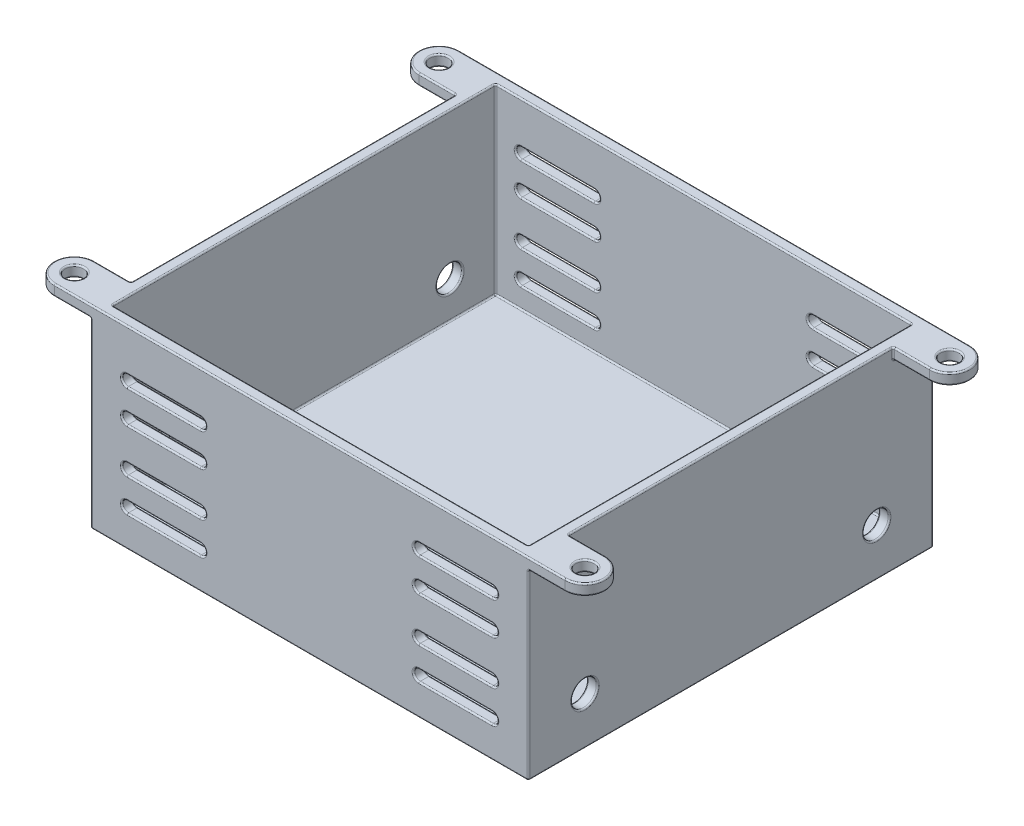
SolidWorks part; units mm, degrees
ref_plane "Front Plane" through (0, 0, 0) normal (0, 0, 1) x (1, 0, 0)
ref_plane "Top Plane" through (0, 0, 0) normal (0, 1, 0) x (1, 0, 0)
ref_plane "Right Plane" through (0, 0, 0) normal (1, 0, 0) x (0, 0, -1)
sketch "Sketch1" plane through (0, 0, 0) normal (0, 1, 0) x (1, 0, 0)
  line L0 (-35, 27.75) -> (35, 27.75) construction
  line L1 (-35, 25) -> (35, 25) construction
  line L2 (-35, 25) -> (-35, -25) construction
  line L3 (-35, -25) -> (35, -25) construction
  line L4 (35, 25) -> (35, -25) construction
  line L5 (-35, 25) -> (35, -25) construction
  line L6 (-35, -25) -> (35, 25) construction
  line L7 (-35, -27.75) -> (35, -27.75) construction
  line L8 (37.75, 25) -> (37.75, -25) construction
  line L9 (-37.75, 25) -> (-37.75, -25) construction
  line L10 (-35, 27.75) -> (-30, 27.75)
  line L11 (-30, 27.75) -> (30, 27.75)
  line L12 (-30, 27.75) -> (-30, -27.75)
  line L13 (-30, -27.75) -> (30, -27.75)
  line L14 (30, 27.75) -> (30, -27.75)
  line L15 (-30, 27.75) -> (30, -27.75) construction
  line L16 (-30, -27.75) -> (30, 27.75) construction
  line L17 (-35, 22.25) -> (-30, 22.25)
  line L18 (35, 27.75) -> (30, 27.75)
  line L19 (35, 22.25) -> (30, 22.25)
  line L20 (30, -27.75) -> (35, -27.75)
  line L21 (35, -22.25) -> (30, -22.25)
  line L22 (-35, -22.25) -> (-30, -22.25)
  line L23 (-35, -27.75) -> (-30, -27.75)
  circle A0 centre (-35, 25) radius 1.25
  circle A1 centre (35, 25) radius 1.25
  circle A2 centre (35, -25) radius 1.25
  circle A3 centre (-35, -25) radius 1.25
  circle A4 centre (35, 25) radius 2.75
  circle A5 centre (35, -25) radius 2.75
  circle A6 centre (-35, -25) radius 2.75
  circle A7 centre (-35, 25) radius 2.75
  point P0 (0, 0)
  point P27 (0, 0)
  dimension "D3" = 2.5
  dimension "D1" = 70
  dimension "D2" = 50
  dimension "D5" = 60
  dimension "D4" = 1.5
sketch "Sketch2" plane through (0, 0, 0) normal (0, 1, 0) x (1, 0, 0)
  line L10 (-30, 27.75) -> (-30, -27.75) construction
  line L11 (-30, -27.75) -> (30, -27.75) construction
  line L12 (30, 27.75) -> (30, -27.75) construction
  line L13 (-30, 27.75) -> (30, 27.75) construction
  line L14 (-28.5, 26.25) -> (-28.5, -26.25)
  line L15 (-28.5, -26.25) -> (28.5, -26.25)
  line L16 (28.5, -26.25) -> (28.5, 26.25)
  line L17 (28.5, 26.25) -> (-28.5, 26.25)
  line L18 (-28.5, 26.25) -> (-28.5, -26.25)
  line L19 (-28.5, -26.25) -> (28.5, -26.25)
  line L20 (28.5, -26.25) -> (28.5, 26.25)
  line L21 (28.5, 26.25) -> (-28.5, 26.25)
  line L22 (-30, 27.75) -> (-30, -27.75)
  line L23 (-30, -27.75) -> (30, -27.75)
  line L24 (30, 27.75) -> (30, -27.75)
  line L25 (-30, 27.75) -> (30, 27.75)
  dimension "D1" = 1.5
extrude "Boss-Extrude1" add sketch "Sketch2" against normal blind 25
sketch "Sketch3" plane through (0, -25, 0) normal (0, -1, 0) x (1, 0, 0)
  line L0 (30, -27.75) -> (-30, -27.75) construction
  line L1 (-30, -27.75) -> (-30, 27.75) construction
  line L2 (-30, 27.75) -> (30, 27.75) construction
  line L3 (30, 27.75) -> (30, -27.75) construction
  line L4 (30, -27.75) -> (-30, -27.75)
  line L5 (-30, -27.75) -> (-30, 27.75)
  line L6 (-30, 27.75) -> (30, 27.75)
  line L7 (30, 27.75) -> (30, -27.75)
extrude "Boss-Extrude2" add sketch "Sketch3" along normal blind 1.5
sketch "Sketch4" plane through (0, 0, 0) normal (0, 1, 0) x (1, 0, 0)
  line L0 (-35, -27.75) -> (-30, -27.75) construction
  line L1 (-35, -22.25) -> (-30, -22.25) construction
  line L2 (30, -27.75) -> (35, -27.75) construction
  line L3 (35, -22.25) -> (30, -22.25) construction
  line L4 (-35, 22.25) -> (-30, 22.25) construction
  line L5 (-35, 27.75) -> (-30, 27.75) construction
  line L6 (35, 22.25) -> (30, 22.25) construction
  line L7 (35, 27.75) -> (30, 27.75) construction
  line L8 (-35, -27.75) -> (-30, -27.75)
  line L9 (-35, -22.25) -> (-30, -22.25)
  line L10 (30, -27.75) -> (35, -27.75)
  line L11 (35, -22.25) -> (30, -22.25)
  line L12 (-35, 22.25) -> (-30, 22.25)
  line L13 (-35, 27.75) -> (-30, 27.75)
  line L14 (35, 22.25) -> (30, 22.25)
  line L15 (35, 27.75) -> (30, 27.75)
  line L16 (-30, 27.75) -> (-30, 22.25)
  line L17 (30, 27.75) -> (30, 22.25)
  line L18 (30, -22.25) -> (30, -27.75)
  line L19 (-30, -22.25) -> (-30, -27.75)
  circle A0 centre (-35, -25) radius 1.25 construction
  circle A1 centre (-35, -25) radius 2.75 construction
  circle A2 centre (35, -25) radius 1.25 construction
  circle A3 centre (35, -25) radius 2.75 construction
  circle A4 centre (-35, 25) radius 2.75 construction
  circle A5 centre (35, 25) radius 1.25 construction
  circle A6 centre (35, 25) radius 2.75 construction
  circle A7 centre (-35, -25) radius 1.25
  arc A8 (-35, -22.25) -> (-35, -27.75) centre (-35, -25) ccw
  circle A9 centre (35, -25) radius 1.25
  arc A10 (35, -27.75) -> (35, -22.25) centre (35, -25) ccw
  arc A11 (-35, 27.75) -> (-35, 22.25) centre (-35, 25) ccw
  circle A12 centre (35, 25) radius 1.25
  arc A13 (35, 22.25) -> (35, 27.75) centre (35, 25) ccw
  circle A14 centre (-35, 25) radius 1.25 construction
  circle A15 centre (-35, 25) radius 1.25
extrude "Boss-Extrude3" add sketch "Sketch4" against normal blind 1.5
sketch "Sketch5" plane through (0, 0, 0) normal (0, 0, 1) x (1, 0, 0)
  line L0 (-30, -14) -> (30, -14) construction
  line L1 (-30, -26.5) -> (-30, -1.5) construction
  line L2 (30, -26.5) -> (30, -1.5) construction
  line L3 (0, -14) -> (0, -21.8638) construction
  line L4 (-25, -6.5) -> (-15, -6.5) construction
  line L5 (-25, -5.75) -> (-15, -5.75)
  line L6 (-25, -7.25) -> (-15, -7.25)
  line L7 (-25, -11) -> (-15, -11) construction
  line L8 (-25, -10.25) -> (-15, -10.25)
  line L9 (-25, -11.75) -> (-15, -11.75)
  line L10 (-25, -21.5) -> (-15, -21.5) construction
  line L11 (-25, -22.25) -> (-15, -22.25)
  line L12 (-25, -20.75) -> (-15, -20.75)
  line L13 (-25, -17) -> (-15, -17) construction
  line L14 (-25, -17.75) -> (-15, -17.75)
  line L15 (-25, -16.25) -> (-15, -16.25)
  line L16 (25, -6.5) -> (15, -6.5) construction
  line L17 (25, -5.75) -> (15, -5.75)
  line L18 (25, -7.25) -> (15, -7.25)
  line L19 (25, -11) -> (15, -11) construction
  line L20 (25, -10.25) -> (15, -10.25)
  line L21 (25, -11.75) -> (15, -11.75)
  line L22 (25, -21.5) -> (15, -21.5) construction
  line L23 (25, -22.25) -> (15, -22.25)
  line L24 (25, -20.75) -> (15, -20.75)
  line L25 (25, -17) -> (15, -17) construction
  line L26 (25, -17.75) -> (15, -17.75)
  line L27 (25, -16.25) -> (15, -16.25)
  arc A0 (-25, -5.75) -> (-25, -7.25) centre (-25, -6.5) ccw
  arc A1 (-15, -7.25) -> (-15, -5.75) centre (-15, -6.5) ccw
  arc A2 (-25, -10.25) -> (-25, -11.75) centre (-25, -11) ccw
  arc A3 (-15, -11.75) -> (-15, -10.25) centre (-15, -11) ccw
  arc A4 (-25, -22.25) -> (-25, -20.75) centre (-25, -21.5) cw
  arc A5 (-15, -20.75) -> (-15, -22.25) centre (-15, -21.5) cw
  arc A6 (-25, -17.75) -> (-25, -16.25) centre (-25, -17) cw
  arc A7 (-15, -16.25) -> (-15, -17.75) centre (-15, -17) cw
  arc A8 (25, -5.75) -> (25, -7.25) centre (25, -6.5) cw
  arc A9 (15, -7.25) -> (15, -5.75) centre (15, -6.5) cw
  arc A10 (25, -10.25) -> (25, -11.75) centre (25, -11) cw
  arc A11 (15, -11.75) -> (15, -10.25) centre (15, -11) cw
  arc A12 (25, -22.25) -> (25, -20.75) centre (25, -21.5) ccw
  arc A13 (15, -20.75) -> (15, -22.25) centre (15, -21.5) ccw
  arc A14 (25, -17.75) -> (25, -16.25) centre (25, -17) ccw
  arc A15 (15, -16.25) -> (15, -17.75) centre (15, -17) ccw
  point P11 (-20, -6.5)
  point P17 (-20, -11)
  point P25 (-20, -21.5)
  point P32 (-20, -17)
  point P39 (20, -6.5)
  point P46 (20, -11)
  point P53 (20, -21.5)
  point P60 (20, -17)
  dimension "D1" = 20
  dimension "D2" = 1.5
  dimension "D3" = 10
  dimension "D4" = 7.5
  dimension "D5" = 4.5
extrude "Cut-Extrude1" cut sketch "Sketch5" against normal through all both and the other way through all
sketch "Sketch6" plane through (0, 0, 0) normal (1, 0, 0) x (0, 0, -1)
  line L0 (0, 0) -> (0, -20) construction
  line L1 (0, -20) -> (-20, -20) construction
  circle A0 centre (-20, -20) radius 1.75
  circle A1 centre (20, -20) radius 1.75
  dimension "D1" = 20
  dimension "D3" = 3.5
  dimension "D2" = 20
extrude "Cut-Extrude2" cut sketch "Sketch6" against normal through all both and the other way through all
fillet "Fillet1" radius 0.2 196 edges at (25.75, -6.5, 26.25) (20, -7.25, 26.25) (14.25, -6.5, 26.25) (20, -5.75, 26.25) (-25.75, -17, 26.25) (-20, -16.25, 26.25) (-14.25, -17, 26.25) (-20, -17.75, 26.25) (-25.75, -21.5, 26.25) (-20, -20.75, 26.25) (-14.25, -21.5, 26.25) (-20, -22.25, 26.25) (-25.75, -11, 26.25) (-20, -10.25, 26.25) (-14.25, -11, 26.25) (-20, -11.75, 26.25) (25.75, -17, 26.25) (20, -17.75, 26.25) (14.25, -17, 26.25) (20, -16.25, 26.25) (25.75, -21.5, 26.25) (20, -22.25, 26.25) (14.25, -21.5, 26.25) (20, -20.75, 26.25) (25.75, -11, 26.25) (20, -11.75, 26.25) (14.25, -11, 26.25) (20, -10.25, 26.25) (-25.75, -6.5, 26.25) (-20, -5.75, 26.25) (-14.25, -6.5, 26.25) (-20, -7.25, 26.25) (30, -14, -27.75) (30, -14, 27.75) (-30, -14, 27.75) (-30, -14, -27.75) (30, 0, 0) (0, 0, 27.75) (-30, 0, 0) (0, 0, -27.75) (28.5, -12.5, -26.25) (28.5, -12.5, 26.25) (-28.5, -12.5, 26.25) (-28.5, -12.5, -26.25) (28.5, -25, 0) (0, -25, 26.25) (-28.5, -25, 0) (0, -25, -26.25) (28.5, 0, 0) (0, 0, 26.25) (-28.5, 0, 0) (0, 0, -26.25) (0, -26.5, -27.75) (-30, -26.5, 0) (0, -26.5, 27.75) (30, -26.5, 0) (-30, -0.75, 22.25) (-32.5, -1.5, 22.25) (-30, -1.5, 25) (-32.5, -1.5, 27.75) (-37.75, -1.5, 25) (-32.5, 0, 22.25) (-37.75, 0, 25) (-35, -1.5, 26.25) (-35, 0, 26.25) (30, -0.75, 22.25) (32.5, -1.5, 22.25) (37.75, -1.5, 25) (32.5, -1.5, 27.75) (30, -1.5, 25) (32.5, 0, 22.25) (37.75, 0, 25) (35, -1.5, 26.25) (35, 0, 26.25) (-30, -0.75, -22.25) (-32.5, -1.5, -27.75) (-30, -1.5, -25) (-32.5, -1.5, -22.25) (-37.75, -1.5, -25) (-32.5, 0, -22.25) (-37.75, 0, -25) (-35, -1.5, -23.75) (-35, 0, -23.75) (30, -0.75, -22.25) (32.5, -1.5, -22.25) (30, -1.5, -25) (32.5, -1.5, -27.75) (37.75, -1.5, -25) (32.5, 0, -22.25) (37.75, 0, -25) (35, -1.5, -23.75) (35, 0, -23.75) (25.75, -6.5, -26.25) (20, -7.25, -26.25) (14.25, -6.5, -26.25) (20, -5.75, -26.25) (-25.75, -17, -26.25) (-20, -16.25, -26.25) (-14.25, -17, -26.25) (-20, -17.75, -26.25) (-25.75, -21.5, -26.25) (-20, -20.75, -26.25) (-14.25, -21.5, -26.25) (-20, -22.25, -26.25) (-25.75, -11, -26.25) (-20, -10.25, -26.25) (-14.25, -11, -26.25) (-20, -11.75, -26.25) (25.75, -17, -26.25) (20, -17.75, -26.25) (14.25, -17, -26.25) (20, -16.25, -26.25) (25.75, -21.5, -26.25) (20, -22.25, -26.25) (14.25, -21.5, -26.25) (20, -20.75, -26.25) (25.75, -11, -26.25) (20, -11.75, -26.25) (14.25, -11, -26.25) (20, -10.25, -26.25) (-25.75, -6.5, -26.25) (-20, -5.75, -26.25) (-14.25, -6.5, -26.25) (-20, -7.25, -26.25) (-20, -5.75, -27.75) (-14.25, -6.5, -27.75) (-20, -7.25, -27.75) (-25.75, -6.5, -27.75) (-20, -5.75, 27.75) (-14.25, -6.5, 27.75) (-20, -7.25, 27.75) (-25.75, -6.5, 27.75) (-20, -10.25, -27.75) (-14.25, -11, -27.75) (-20, -11.75, -27.75) (-25.75, -11, -27.75) (-20, -10.25, 27.75) (-14.25, -11, 27.75) (-20, -11.75, 27.75) (-25.75, -11, 27.75) (-20, -20.75, -27.75) (-14.25, -21.5, -27.75) (-20, -22.25, -27.75) (-25.75, -21.5, -27.75) (-20, -20.75, 27.75) (-14.25, -21.5, 27.75) (-20, -22.25, 27.75) (-25.75, -21.5, 27.75) (-20, -16.25, -27.75) (-14.25, -17, -27.75) (-20, -17.75, -27.75) (-25.75, -17, -27.75) (-20, -16.25, 27.75) (-14.25, -17, 27.75) (-20, -17.75, 27.75) (-25.75, -17, 27.75) (20, -7.25, -27.75) (14.25, -6.5, -27.75) (20, -5.75, -27.75) (25.75, -6.5, -27.75) (20, -7.25, 27.75) (14.25, -6.5, 27.75) (20, -5.75, 27.75) (25.75, -6.5, 27.75) (20, -11.75, -27.75) (14.25, -11, -27.75) (20, -10.25, -27.75) (25.75, -11, -27.75) (20, -11.75, 27.75) (14.25, -11, 27.75) (20, -10.25, 27.75) (25.75, -11, 27.75) (20, -22.25, -27.75) (14.25, -21.5, -27.75) (20, -20.75, -27.75) (25.75, -21.5, -27.75) (20, -22.25, 27.75) (14.25, -21.5, 27.75) (20, -20.75, 27.75) (25.75, -21.5, 27.75) (20, -17.75, -27.75) (14.25, -17, -27.75) (20, -16.25, -27.75) (25.75, -17, -27.75) (20, -17.75, 27.75) (14.25, -17, 27.75) (20, -16.25, 27.75) (25.75, -17, 27.75) (-30, -20, 21.75) (30, -20, 18.25) (28.5, -20, 18.25) (-28.5, -20, 21.75) (-30, -20, -18.25) (30, -20, -21.75) (28.5, -20, -21.75) (-28.5, -20, -18.25)
